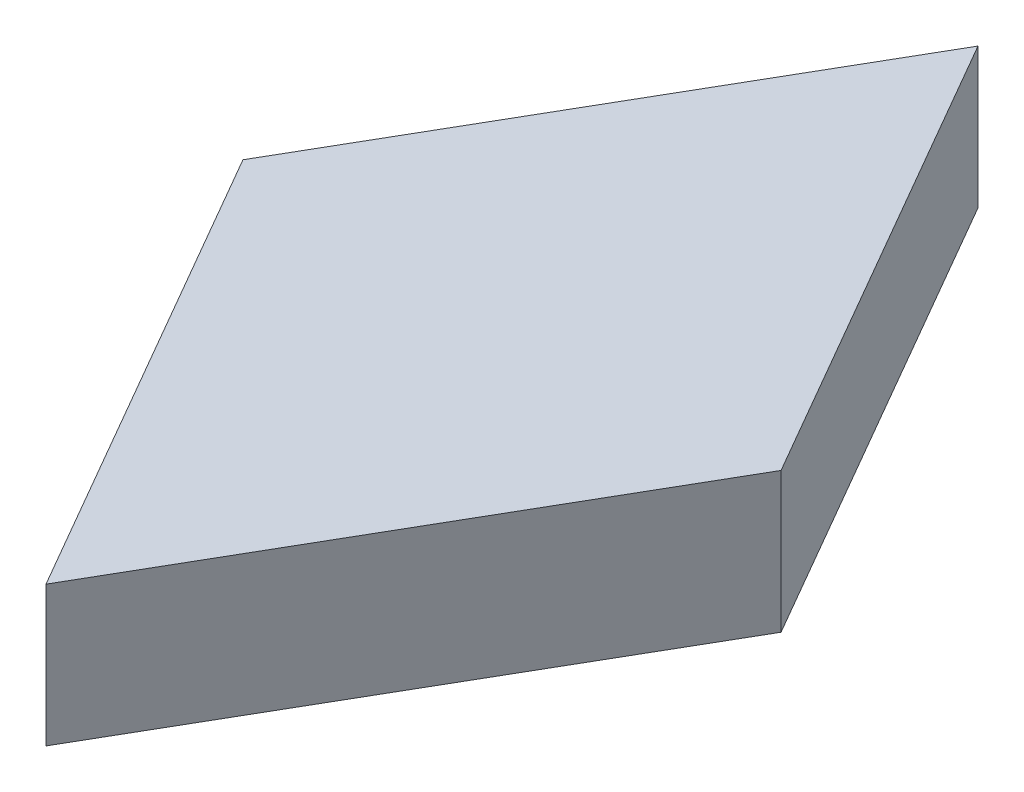
SolidWorks part; units mm, degrees
ref_plane "Front Plane" through (0, 0, 0) normal (0, 0, 1) x (1, 0, 0)
ref_plane "Top Plane" through (0, 0, 0) normal (0, 1, 0) x (1, 0, 0)
ref_plane "Right Plane" through (0, 0, 0) normal (1, 0, 0) x (0, 0, -1)
sketch "Sketch1" plane through (0, 0, 0) normal (0, 1, 0) x (1, 0, 0)
  line L0 (0, 6.6511) -> (-3.84, 0)
  line L1 (-3.84, 0) -> (0, -6.6511)
  line L2 (0, -6.6511) -> (3.84, 0)
  line L3 (3.84, 0) -> (0, 6.6511)
  line L4 (-3.84, 0) -> (3.84, 0) construction
  line L5 (0, 6.6511) -> (0, -6.6511) construction
  point P5 (0, 0)
  dimension "D1" = 60
  dimension "D2" = 60
  dimension "D3" = 120
  dimension "D4" = 7.68
extrude "Boss-Extrude1" add sketch "Sketch1" along normal blind 2 contours L3 L0 L1 L2
sketch "Sketch2" plane through (0, 0, 0) normal (0, -1, 0) x (-1, 0, 0)
  circle A0 centre (0, 0) radius 1.5
  dimension "D1" = 3
extrude "Cut-Extrude1" cut sketch "Sketch2" against normal blind 1
